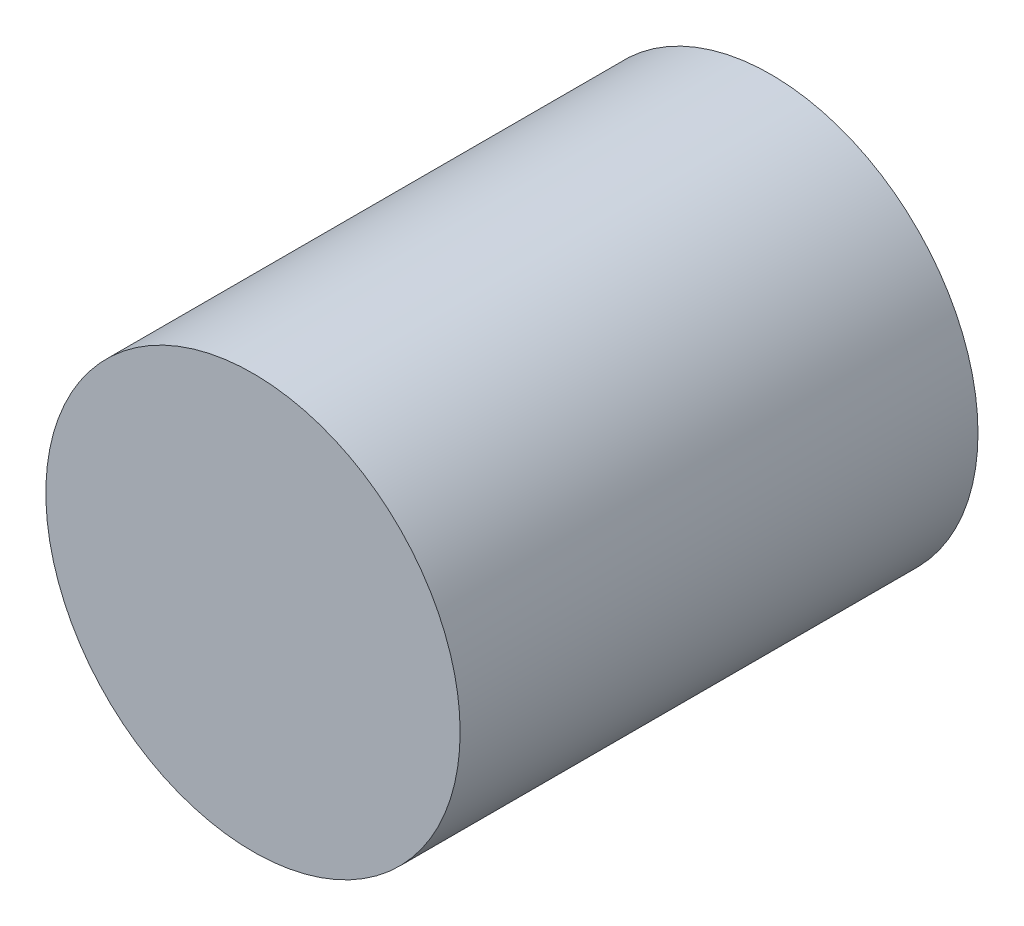
SolidWorks part; units mm, degrees
ref_plane "Front Plane" through (0, 0, 0) normal (0, 0, 1) x (1, 0, 0)
ref_plane "Top Plane" through (0, 0, 0) normal (0, 1, 0) x (1, 0, 0)
ref_plane "Right Plane" through (0, 0, 0) normal (1, 0, 0) x (0, 0, -1)
sketch "Sketch1" plane through (0, 0, 0) normal (0, 0, 1) x (1, 0, 0)
  circle A0 centre (0, 0) radius 10
  dimension "D1" = 20
extrude "Boss-Extrude1" add sketch "Sketch1" along normal mid plane 25
